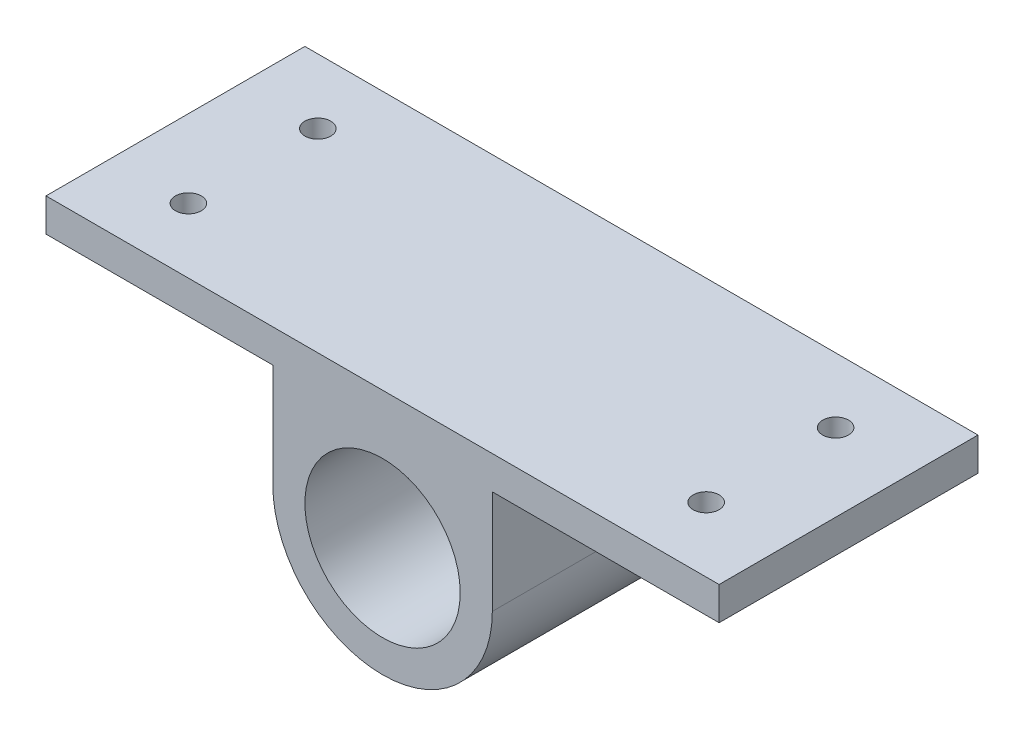
SolidWorks part; units mm, degrees
ref_plane "Front Plane" through (0, 0, 0) normal (0, 0, 1) x (1, 0, 0)
ref_plane "Top Plane" through (0, 0, 0) normal (0, 1, 0) x (1, 0, 0)
ref_plane "Right Plane" through (0, 0, 0) normal (1, 0, 0) x (0, 0, -1)
sketch "Sketch1" plane through (0, 0, 0) normal (0, 0, 1) x (1, 0, 0)
  line L0 (325, 0) -> (-325, 0)
  line L1 (-325, 0) -> (-325, -32)
  line L2 (-325, -32) -> (-106, -32)
  line L3 (0, 0) -> (0, -132)
  line L4 (-106, -132) -> (-106, -32)
  line L6 (106, -132) -> (106, -32)
  line L7 (325, -32) -> (106, -32)
  line L8 (325, 0) -> (325, -32)
  circle A0 centre (0, -132) radius 75
  arc A1 (-106, -132) -> (106, -132) centre (0, -132) ccw
  point P7 (0, 0)
  dimension "D3" = 150
  dimension "D4" = 212
  dimension "D2" = 32
  dimension "D5" = 132
extrude "Boss-Extrude1" add sketch "Sketch1" along normal blind 250
sketch "Sketch2" plane through (0, 0, 0) normal (0, 1, 0) x (1, 0, 0)
  line L0 (-325, -250) -> (-325, 0) construction
  line L1 (325, -250) -> (-325, -250) construction
  line L2 (0, 0) -> (0, -276.4806) construction
  circle A0 centre (-250, -187.5) radius 12.5
  circle A1 centre (-250, -62.5) radius 12.5
  circle A2 centre (250, -187.5) radius 12.5
  circle A3 centre (250, -62.5) radius 12.5
  dimension "D1" = 25
  dimension "D2" = 25
  dimension "D3" = 75
  dimension "D4" = 125
  dimension "D5" = 62.5
extrude "Cut-Extrude1" cut sketch "Sketch2" against normal blind 250
